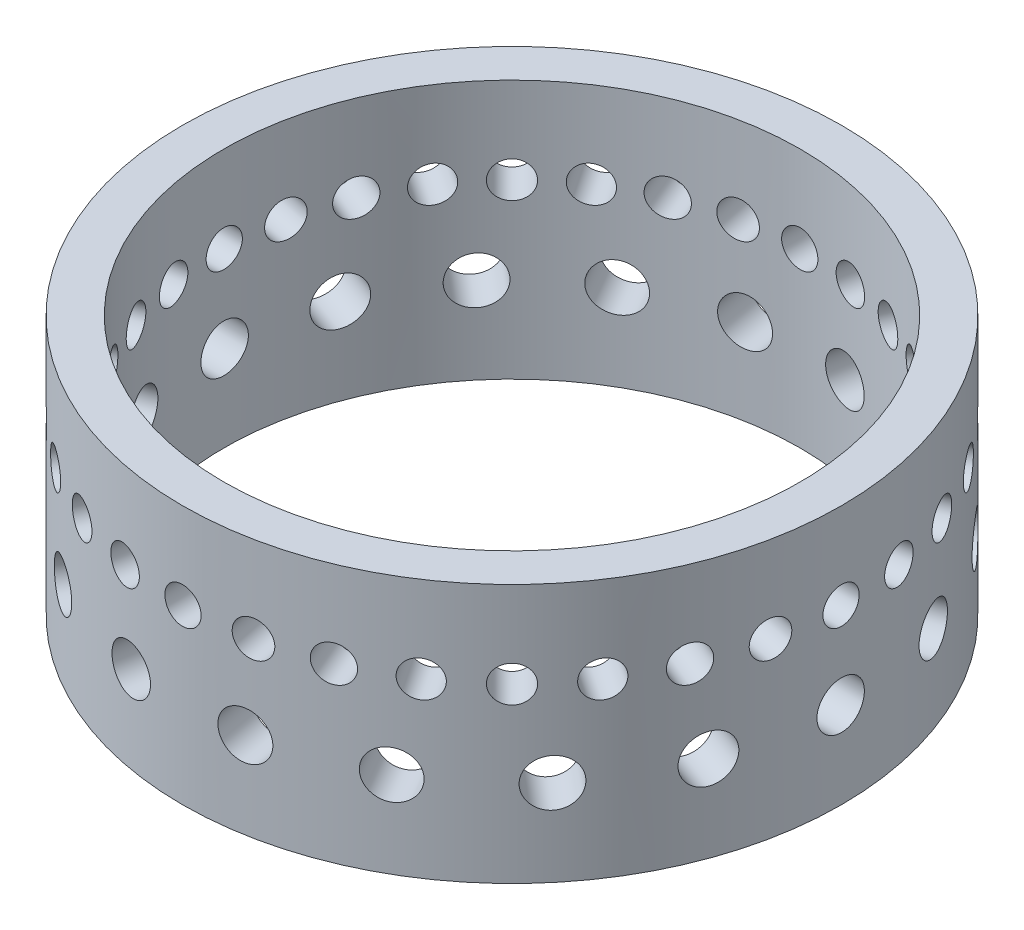
SolidWorks part; units mm, degrees
ref_plane "Front Plane" through (0, 0, 0) normal (0, 0, 1) x (1, 0, 0)
ref_plane "Top Plane" through (0, 0, 0) normal (0, 1, 0) x (1, 0, 0)
ref_plane "Right Plane" through (0, 0, 0) normal (1, 0, 0) x (0, 0, -1)
sketch "Sketch1" plane through (0, 0, 0) normal (0, 1, 0) x (1, 0, 0)
  circle A0 centre (0, 0) radius 25.4
  circle A1 centre (0, 0) radius 22.225
  dimension "D1" = 50.8
  dimension "D2" = 44.45
extrude "Boss-Extrude1" add sketch "Sketch1" along normal blind 19.9644
sketch "Sketch2" plane through (0, 0, 0) normal (1, 0, 0) x (0, 0, -1)
  line L0 (-25.4, 0) -> (25.4, 0) construction
  circle A0 centre (0, 6.6548) radius 1.8288
  dimension "D1" = 3.6576
  dimension "D2" = 6.6548
extrude "Cut-Extrude1" cut sketch "Sketch2" against normal blind 35.4584
sketch "Sketch3" plane through (0, 0, 0) normal (1, 0, 0) x (0, 0, -1)
  line L0 (0, 0) -> (0, 23.7408) construction
pattern_circular "CirPattern1" count 18 over 360 about axis through (0, 0, 0) along (0, 1, 0) of "Cut-Extrude1"
sketch "Sketch4" plane through (0, 0, 0) normal (1, 0, 0) x (0, 0, -1)
  line L0 (0, 0) -> (0, 23.7408) construction
  line L1 (22.225, 19.9644) -> (-22.225, 19.9644) construction
  circle A0 centre (0, 13.3096) radius 1.397
  dimension "D1" = 2.794
  dimension "D2" = 6.6548
extrude "Cut-Extrude2" cut sketch "Sketch4" against normal blind 35.4584
pattern_circular "CirPattern2" count 32 over 360 about axis through (0, 0, 0) along (0, 1, 0) of "Cut-Extrude2"
